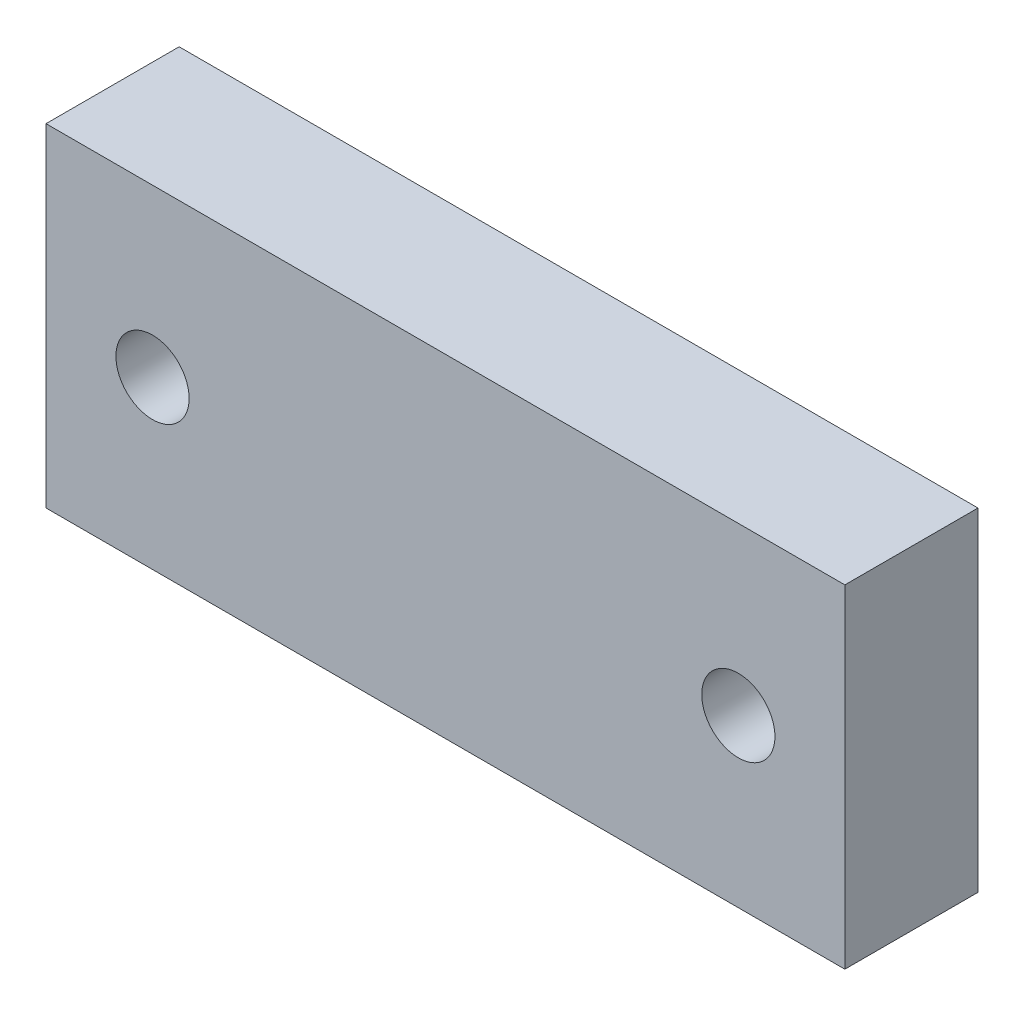
SolidWorks part; units mm, degrees
ref_plane "前基準面" through (0, 0, 0) normal (0, 0, 1) x (1, 0, 0)
ref_plane "上基準面" through (0, 0, 0) normal (0, 1, 0) x (1, 0, 0)
ref_plane "右基準面" through (0, 0, 0) normal (1, 0, 0) x (0, 0, -1)
sketch "草圖1" plane through (0, 0, 0) normal (0, 0, 1) x (1, 0, 0)
  line L1 (-13.0039, 18.0012) -> (46.9961, 18.0012)
  line L2 (-13.0039, 18.0012) -> (-13.0039, -6.9988)
  line L3 (-13.0039, -6.9988) -> (46.9961, -6.9988)
  line L4 (46.9961, 18.0012) -> (46.9961, -6.9988)
  circle A0 centre (-5.0039, 5.5012) radius 2.75
  circle A1 centre (38.9961, 5.5012) radius 2.75
  dimension "D1" = 5.5
  dimension "D2" = 5.5
  dimension "D3" = 44
  dimension "D4" = 8
  dimension "D5" = 8
  dimension "D6" = 25
  dimension "D7" = 12.5
extrude "填料-伸長1" add sketch "草圖1" along normal blind 10
